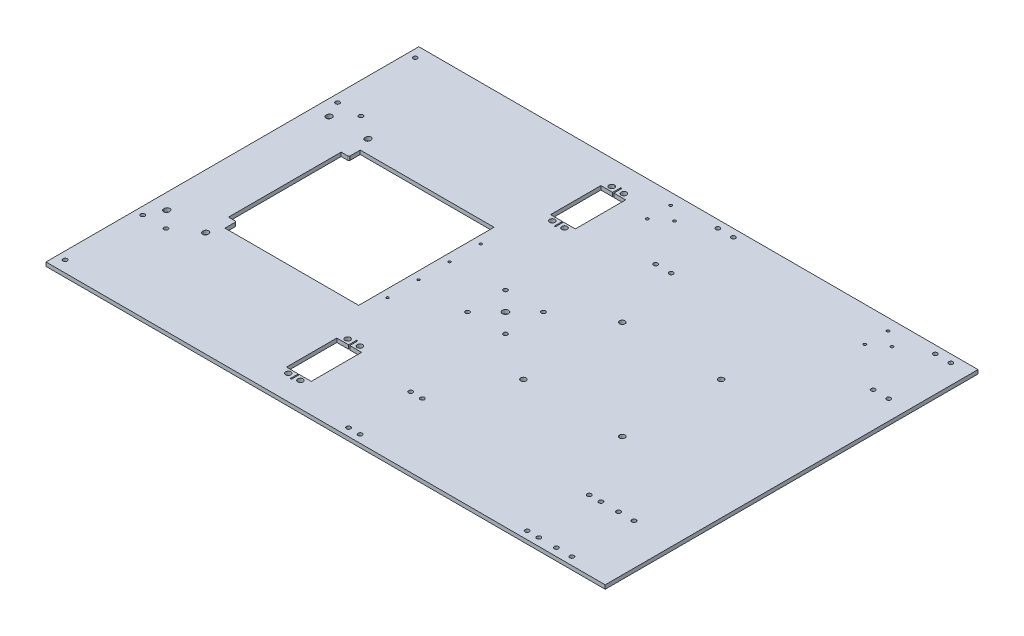
SolidWorks part; units mm, degrees
ref_plane "Front Plane" through (0, 0, 0) normal (0, 0, 1) x (1, 0, 0)
ref_plane "Top Plane" through (0, 0, 0) normal (0, 1, 0) x (1, 0, 0)
ref_plane "Right Plane" through (0, 0, 0) normal (1, 0, 0) x (0, 0, -1)
sketch "Sketch1" plane through (0, 0, 0) normal (0, 1, 0) x (1, 0, 0)
  line L1 (-228.6, -152.4) -> (228.6, -152.4)
  line L2 (-228.6, -152.4) -> (-228.6, 152.4)
  line L3 (-228.6, 152.4) -> (228.6, 152.4)
  line L4 (228.6, -152.4) -> (228.6, 152.4)
  line L5 (-228.6, -152.4) -> (228.6, 152.4) construction
  line L6 (-228.6, 152.4) -> (228.6, -152.4) construction
  point P0 (0, 0)
  dimension "D1" = 304.8
  dimension "D2" = 457.2
extrude "Boss-Extrude1" add sketch "Sketch1" along normal blind 3.175 contours L3 L4 L1 L2
sketch "Sketch2" plane through (0, 3.175, 0) normal (0, 1, 0) x (1, 0, 0)
  line L0 (-215.9, 66.04) -> (-215.9, 66.675) construction
  line L1 (-218.1, 66.04) -> (-218.1, 66.675)
  line L2 (-213.7, 66.04) -> (-213.7, 66.675)
  line L3 (-184.15, 66.04) -> (-184.15, 66.675) construction
  line L4 (-186.35, 66.04) -> (-186.35, 66.675)
  line L5 (-181.95, 66.04) -> (-181.95, 66.675)
  line L6 (-215.9, -66.04) -> (-215.9, -66.675) construction
  line L7 (-213.7, -66.04) -> (-213.7, -66.675)
  line L8 (-218.1, -66.04) -> (-218.1, -66.675)
  line L9 (-184.15, -66.04) -> (-184.15, -66.675) construction
  line L10 (-181.95, -66.04) -> (-181.95, -66.675)
  line L11 (-186.35, -66.04) -> (-186.35, -66.675)
  circle A0 centre (-184.15, -66.675) radius 2.2 construction
  circle A1 centre (-215.9, -66.675) radius 2.2 construction
  circle A2 centre (-184.15, 66.675) radius 2.2 construction
  circle A3 centre (-215.9, 66.675) radius 2.2 construction
  circle A6 centre (-184.15, -66.675) radius 2.2 construction
  circle A7 centre (-215.9, -66.675) radius 2.2 construction
  circle A8 centre (-184.15, 66.675) radius 2.2 construction
  circle A9 centre (-215.9, 66.675) radius 2.2 construction
  arc A10 (-218.1, 66.04) -> (-213.7, 66.04) centre (-215.9, 66.04) ccw
  arc A11 (-213.7, 66.675) -> (-218.1, 66.675) centre (-215.9, 66.675) ccw
  arc A12 (-186.35, 66.04) -> (-181.95, 66.04) centre (-184.15, 66.04) ccw
  arc A13 (-181.95, 66.675) -> (-186.35, 66.675) centre (-184.15, 66.675) ccw
  arc A14 (-213.7, -66.04) -> (-218.1, -66.04) centre (-215.9, -66.04) ccw
  arc A15 (-218.1, -66.675) -> (-213.7, -66.675) centre (-215.9, -66.675) ccw
  arc A16 (-181.95, -66.04) -> (-186.35, -66.04) centre (-184.15, -66.04) ccw
  arc A17 (-186.35, -66.675) -> (-181.95, -66.675) centre (-184.15, -66.675) ccw
  point P9 (-215.9, 66.3575)
  point P19 (-184.15, 66.3575)
  point P25 (-215.9, -66.3575)
  point P30 (-184.15, -66.3575)
  dimension "D1" = 0.635
extrude "Cut-Extrude1" cut sketch "Sketch2" against normal through all
sketch "Sketch3" plane through (0, 3.175, 0) normal (0, 1, 0) x (1, 0, 0)
  line L0 (-228.6, 0) -> (228.6, 0) construction
  line L1 (-228.6, -152.4) -> (-228.6, 152.4) construction
  line L2 (228.6, -152.4) -> (228.6, 152.4) construction
sketch "Sketch4" plane through (0, 3.175, 0) normal (0, 1, 0) x (1, 0, 0)
  line L0 (-185.7375, 46.0375) -> (-185.7375, -46.0375)
  line L1 (-185.7375, -46.0375) -> (-180.34, -46.0375)
  line L2 (-179.3875, -46.99) -> (-179.3875, -55.3085)
  line L3 (-179.3875, -55.3085) -> (-70.0405, -55.3085)
  line L4 (-70.0405, -55.3085) -> (-70.0405, 55.3085)
  line L5 (-70.0405, 55.3085) -> (-179.3875, 55.3085)
  line L6 (-179.3875, 55.3085) -> (-179.3875, 46.99)
  line L7 (-180.34, 46.0375) -> (-185.7375, 46.0375)
  line L8 (-184.15, 44.45) -> (-184.15, -44.45)
  line L9 (-180.34, 44.45) -> (-184.15, 44.45)
  line L10 (-177.8, 53.721) -> (-177.8, 46.99)
  line L11 (-71.628, 53.721) -> (-177.8, 53.721)
  line L12 (-71.628, -53.721) -> (-71.628, 53.721)
  line L13 (-177.8, -53.721) -> (-71.628, -53.721)
  line L14 (-177.8, -46.99) -> (-177.8, -53.721)
  line L15 (-184.15, -44.45) -> (-180.34, -44.45)
  line L16 (-184.15, 44.45) -> (-184.15, -44.45) construction
  line L17 (-180.34, 44.45) -> (-184.15, 44.45) construction
  line L18 (-177.8, 53.721) -> (-177.8, 46.99) construction
  line L19 (-71.628, 53.721) -> (-177.8, 53.721) construction
  line L20 (-71.628, -53.721) -> (-71.628, 53.721) construction
  line L21 (-177.8, -53.721) -> (-71.628, -53.721) construction
  line L22 (-177.8, -46.99) -> (-177.8, -53.721) construction
  line L23 (-184.15, -44.45) -> (-180.34, -44.45) construction
  arc A0 (-179.3875, -46.99) -> (-180.34, -46.0375) centre (-180.34, -46.99) ccw
  arc A1 (-180.34, 46.0375) -> (-179.3875, 46.99) centre (-180.34, 46.99) ccw
  arc A2 (-180.34, 44.45) -> (-177.8, 46.99) centre (-180.34, 46.99) ccw
  arc A3 (-177.8, -46.99) -> (-180.34, -44.45) centre (-180.34, -46.99) ccw
  arc A4 (-180.34, 44.45) -> (-177.8, 46.99) centre (-180.34, 46.99) ccw construction
  arc A5 (-177.8, -46.99) -> (-180.34, -44.45) centre (-180.34, -46.99) ccw construction
  dimension "D1" = 0
  dimension "D2" = 1.5875
extrude "Cut-Extrude2" cut sketch "Sketch4" against normal up to next
sketch "Sketch5" plane through (0, 3.175, 0) normal (0, 1, 0) x (1, 0, 0)
  circle A0 centre (-203.2, 79.629) radius 1.7 construction
  circle A1 centre (-222.25, 143.129) radius 1.7 construction
  circle A2 centre (-222.25, 79.629) radius 1.7 construction
  circle A3 centre (-203.2, -79.629) radius 1.7 construction
  circle A4 centre (-222.25, -79.629) radius 1.7 construction
  circle A5 centre (-222.25, -143.129) radius 1.7 construction
  circle A6 centre (-203.2, 79.629) radius 1.7
  circle A7 centre (-222.25, 143.129) radius 1.7
  circle A8 centre (-222.25, 79.629) radius 1.7
  circle A9 centre (-203.2, -79.629) radius 1.7
  circle A10 centre (-222.25, -79.629) radius 1.7
  circle A11 centre (-222.25, -143.129) radius 1.7
extrude "Cut-Extrude3" cut sketch "Sketch5" against normal through all
sketch "Sketch7" plane through (0, 3.175, 0) normal (0, 1, 0) x (1, 0, 0)
  line L0 (-55.847, -87.373) -> (-35.593, -128.527) construction
  line L1 (-55.847, -87.373) -> (-46.22, -87.373)
  line L2 (-55.847, -87.373) -> (-55.847, -128.527)
  line L3 (-55.847, -128.527) -> (-46.22, -128.527)
  line L4 (-35.593, -87.373) -> (-35.593, -128.527)
  line L5 (-35.593, -87.373) -> (-55.847, -128.527) construction
  line L6 (-50.72, -83.65) -> (-40.72, -132.25) construction
  line L7 (-50.72, -132.25) -> (-40.72, -83.65) construction
  line L9 (-228.6, -152.4) -> (228.6, -152.4) construction
  line L10 (-45.22, -128.527) -> (-35.593, -128.527)
  line L12 (-46.22, -128.527) -> (-46.22, -135.131)
  line L13 (-46.22, -135.131) -> (-45.22, -135.131)
  line L14 (-45.22, -128.527) -> (-45.22, -135.131)
  line L15 (-45.72, -107.95) -> (-2.6371, -107.95) construction
  line L16 (-46.22, -80.769) -> (-45.22, -80.769)
  line L17 (-46.22, -87.373) -> (-46.22, -80.769)
  line L18 (-45.22, -87.373) -> (-45.22, -80.769)
  line L19 (-45.22, -87.373) -> (-35.593, -87.373)
  line L20 (-228.6, -152.4) -> (-228.6, 152.4) construction
  circle A0 centre (-50.72, -132.25) radius 2.2
  circle A1 centre (-40.72, -132.25) radius 2.2
  circle A2 centre (-50.72, -83.65) radius 2.2
  circle A3 centre (-40.72, -83.65) radius 2.2
  point P8 (-45.72, -135.131)
  point P17 (-45.72, -107.95)
  point P18 (-45.72, -107.95)
  dimension "D5" = 4.4
  dimension "D2" = 10
  dimension "D4" = 48.6
  dimension "D1" = 41.154
  dimension "D3" = 20.254
  dimension "D6" = 44.45
  dimension "D7" = 1
  dimension "D8" = 6.604
  dimension "D9" = 182.88
extrude "Cut-Extrude5" cut sketch "Sketch7" against normal through all
mirror "Mirror1" about plane through (0, 0, 0) normal (0, 0, 1) of "Cut-Extrude5"
sketch "Sketch8" plane through (0, 3.175, 0) normal (0, 1, 0) x (1, 0, 0)
  circle A1 centre (-63.6905, -38.1) radius 1
  circle A2 centre (-63.6905, -38.1) radius 1
  circle A3 centre (-63.6905, -12.7) radius 1
  circle A4 centre (-63.6905, -12.7) radius 1
  circle A5 centre (-63.6905, 12.7) radius 1
  circle A6 centre (-63.6905, 12.7) radius 1
  circle A7 centre (-63.6905, 38.1) radius 1
  circle A8 centre (-63.6905, 38.1) radius 1
  dimension "D1" = 0
  dimension "D2" = 0
  dimension "D3" = 0
  dimension "D4" = 0
extrude "Cut-Extrude6" cut sketch "Sketch8" against normal through all
sketch "Sketch12" plane through (0, 3.175, 0) normal (0, 1, 0) x (1, 0, 0)
  circle A0 centre (195.024, -95.25) radius 1.7 construction
  circle A1 centre (182.324, -95.25) radius 1.7 construction
  circle A2 centre (195.024, -146.05) radius 1.7 construction
  circle A3 centre (182.324, -146.05) radius 1.7 construction
  circle A4 centre (167.9575, -95.25) radius 1.7 construction
  circle A5 centre (158.4325, -95.25) radius 1.7 construction
  circle A6 centre (167.9575, -146.05) radius 1.7 construction
  circle A7 centre (158.4325, -146.05) radius 1.7 construction
  circle A8 centre (21.9075, -146.05) radius 1.7 construction
  circle A9 centre (12.3825, -146.05) radius 1.7 construction
  circle A10 centre (12.3825, -95.25) radius 1.7 construction
  circle A11 centre (21.9075, -95.25) radius 1.7 construction
  circle A12 centre (195.024, -95.25) radius 1.7
  circle A13 centre (182.324, -95.25) radius 1.7
  circle A14 centre (195.024, -146.05) radius 1.7
  circle A15 centre (182.324, -146.05) radius 1.7
  circle A16 centre (167.9575, -95.25) radius 1.7
  circle A17 centre (158.4325, -95.25) radius 1.7
  circle A18 centre (167.9575, -146.05) radius 1.7
  circle A19 centre (158.4325, -146.05) radius 1.7
  circle A20 centre (21.9075, -146.05) radius 1.7
  circle A21 centre (12.3825, -146.05) radius 1.7
  circle A22 centre (12.3825, -95.25) radius 1.7
  circle A23 centre (21.9075, -95.25) radius 1.7
extrude "Cut-Extrude7" cut sketch "Sketch12" against normal through all
sketch "Sketch13" plane through (0, 3.175, 0) normal (0, 1, 0) x (1, 0, 0)
  circle A1 centre (212.725, 95.25) radius 1.7
  circle A2 centre (212.725, 95.25) radius 1.7
  circle A3 centre (212.725, 146.05) radius 1.7
  circle A4 centre (212.725, 146.05) radius 1.7
  circle A5 centre (200.025, 95.25) radius 1.7
  circle A6 centre (200.025, 95.25) radius 1.7
  circle A7 centre (200.025, 146.05) radius 1.7
  circle A8 centre (200.025, 146.05) radius 1.7
  circle A9 centre (177.213, 133.477) radius 1.127
  circle A10 centre (177.213, 133.477) radius 1.127
  circle A11 centre (164.513, 143.002) radius 1.127
  circle A12 centre (164.513, 143.002) radius 1.127
  circle A13 centre (164.513, 123.952) radius 1.127
  circle A14 centre (164.513, 123.952) radius 1.127
  circle A15 centre (34.925, 95.25) radius 1.7
  circle A16 centre (34.925, 95.25) radius 1.7
  circle A17 centre (34.925, 146.05) radius 1.7
  circle A18 centre (34.925, 146.05) radius 1.7
  circle A19 centre (22.225, 95.25) radius 1.7
  circle A20 centre (22.225, 95.25) radius 1.7
  circle A21 centre (22.225, 146.05) radius 1.7
  circle A22 centre (22.225, 146.05) radius 1.7
  circle A23 centre (-0.587, 133.477) radius 1.127
  circle A24 centre (-0.587, 133.477) radius 1.127
  circle A25 centre (-13.287, 143.002) radius 1.127
  circle A26 centre (-13.287, 143.002) radius 1.127
  circle A27 centre (-13.287, 123.952) radius 1.127
  circle A28 centre (-13.287, 123.952) radius 1.127
  dimension "D1" = 0
  dimension "D2" = 0
  dimension "D3" = 0
  dimension "D4" = 0
  dimension "D5" = 0
  dimension "D6" = 0
  dimension "D7" = 0
  dimension "D8" = 0
  dimension "D9" = 0
  dimension "D10" = 0
  dimension "D11" = 0
  dimension "D12" = 0
  dimension "D13" = 0
  dimension "D14" = 0
extrude "Cut-Extrude8" cut sketch "Sketch13" against normal through all
sketch "Sketch14" plane through (0, 3.175, 0) normal (0, 1, 0) x (1, 0, 0)
  line L0 (-20.834, -15.5) -> (10.166, -15.5) construction
  line L1 (49.7588, -40.4112) -> (130.5812, -40.4112) construction
  line L2 (49.7588, -40.4112) -> (49.7588, 40.4112) construction
  line L3 (49.7588, 40.4112) -> (130.5812, 40.4112) construction
  line L4 (130.5812, -40.4112) -> (130.5812, 40.4112) construction
  line L5 (49.7588, -40.4112) -> (130.5812, 40.4112) construction
  line L6 (49.7588, 40.4112) -> (130.5812, -40.4112) construction
  line L7 (-20.834, -15.5) -> (-20.834, 15.5) construction
  line L8 (-20.834, 15.5) -> (10.166, 15.5) construction
  line L9 (10.166, -15.5) -> (10.166, 15.5) construction
  line L10 (-20.834, -15.5) -> (10.166, 15.5) construction
  line L11 (-20.834, 15.5) -> (10.166, -15.5) construction
  circle A0 centre (90.17, 0) radius 9.525 construction
  circle A1 centre (-5.334, 0) radius 2.6035 construction
  circle A2 centre (90.17, 0) radius 9.525 construction
  circle A3 centre (-5.334, 0) radius 2.6035 construction
  circle A4 centre (49.7588, 40.4112) radius 2.2
  circle A5 centre (130.5812, 40.4112) radius 2.2
  circle A7 centre (49.7588, -40.4112) radius 2.2
  circle A9 centre (130.5812, -40.4112) radius 2.2
  circle A12 centre (-20.834, 15.5) radius 1.7
  circle A13 centre (10.166, 15.5) radius 1.7
  circle A14 centre (-20.834, -15.5) radius 1.7
  circle A15 centre (10.166, -15.5) radius 1.7
  circle A16 centre (-5.334, 0) radius 2.5
  dimension "D2" = 4.4
  dimension "D5" = 3.4
  dimension "D6" = 5
  dimension "D4" = 31
  dimension "D1" = 114.3
extrude "Cut-Extrude9" cut sketch "Sketch14" against normal through all
equation "\"tightTol\"= 0.005in"
equation "\"normTol\"= 0.01in"
equation "\"looseTol\"= 0.02in"
equation "\"D2@Sketch4\"=1/16"
equation "\"D2@Sketch14\"=4.4mm"
equation "\"D5@Sketch7\"=4.4mm"
